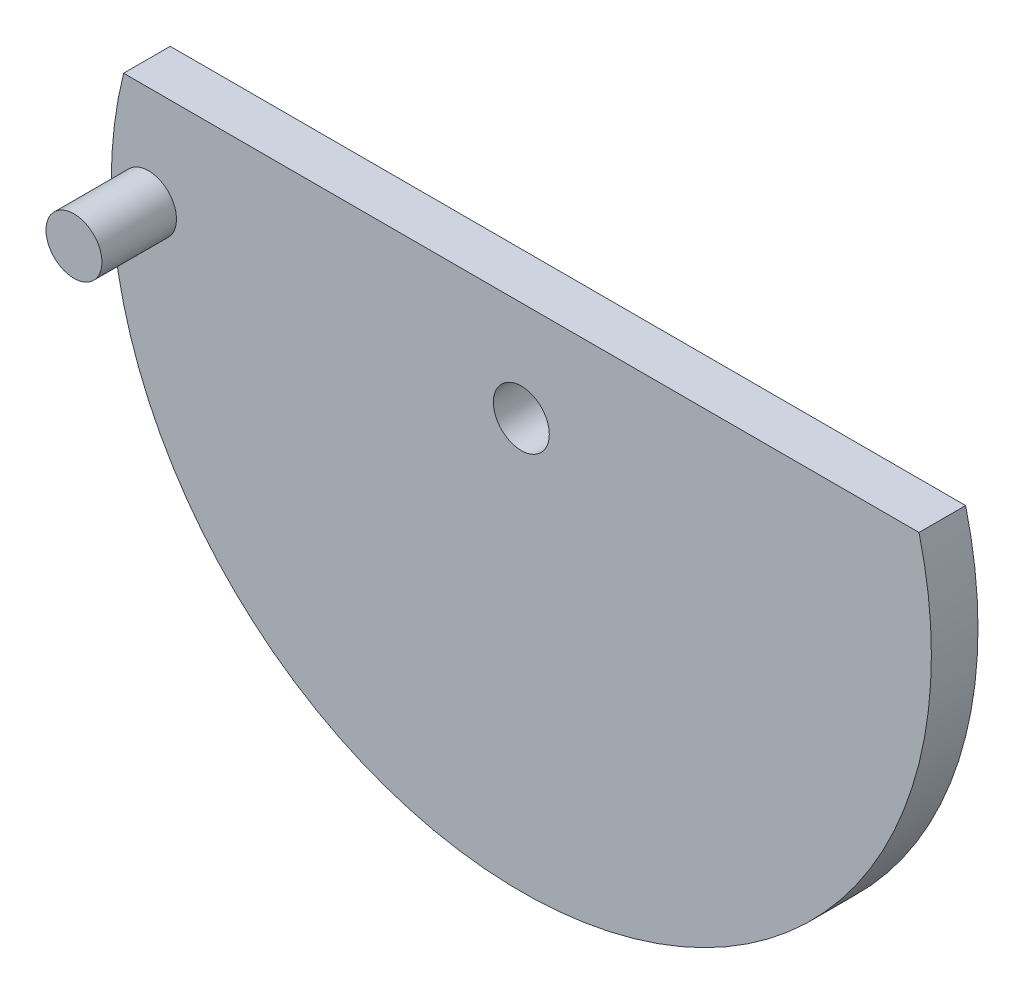
SolidWorks part; units mm, degrees
ref_plane "Front Plane" through (0, 0, 0) normal (0, 0, 1) x (1, 0, 0)
ref_plane "Top Plane" through (0, 0, 0) normal (0, 1, 0) x (1, 0, 0)
ref_plane "Right Plane" through (0, 0, 0) normal (1, 0, 0) x (0, 0, -1)
sketch "Sketch1" plane through (0, 0, 0) normal (0, 0, 1) x (1, 0, 0)
  line L0 (-21.3359, 13.6823) -> (21.3359, 13.6823)
  arc A0 (21.3359, 13.6823) -> (-21.3359, 13.6823) centre (0, 8.3177) cw
  circle A1 centre (0, 8.3177) radius 1.5
extrude "Boss-Extrude1" add sketch "Sketch1" along normal blind 2.5
sketch "Sketch2" plane through (0, 0, 2.5) normal (0, 0, 1) x (1, 0, 0)
  line L0 (0, 8.3177) -> (-20, 8.3177) construction
  circle A0 centre (-20, 8.3177) radius 1.5
  dimension "D1" = 3
  dimension "D2" = 20
extrude "Boss-Extrude2" add sketch "Sketch2" along normal blind 4
